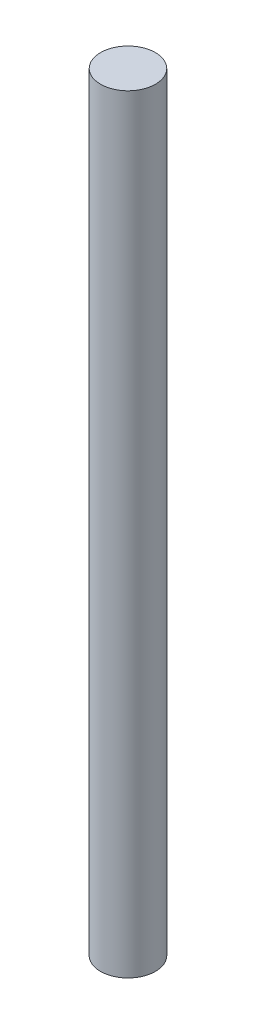
SolidWorks part; units mm, degrees
ref_plane "Front Plane" through (0, 0, 0) normal (0, 0, 1) x (1, 0, 0)
ref_plane "Top Plane" through (0, 0, 0) normal (0, 1, 0) x (1, 0, 0)
ref_plane "Right Plane" through (0, 0, 0) normal (1, 0, 0) x (0, 0, -1)
sketch "Sketch1" plane through (0, 0, 0) normal (0, 1, 0) x (1, 0, 0)
  circle A0 centre (0, 0) radius 3.175
  dimension "D1" = 6.35
extrude "Boss-Extrude1" add sketch "Sketch1" along normal blind 88.9 contours A0
